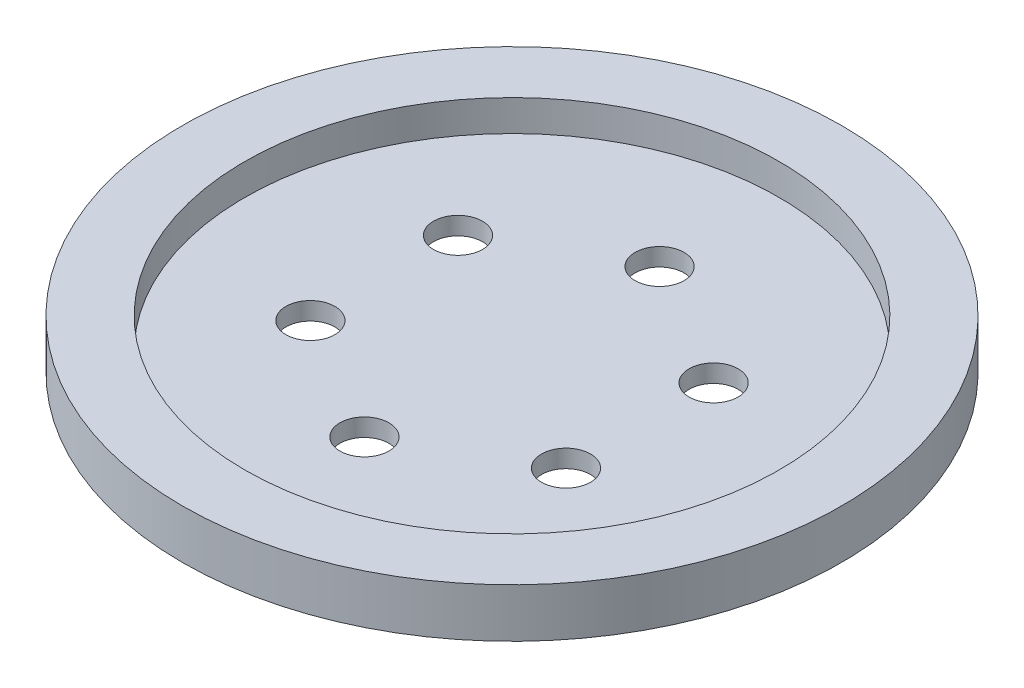
SolidWorks part; units mm, degrees
ref_plane "Front Plane" through (0, 0, 0) normal (0, 0, 1) x (1, 0, 0)
ref_plane "Top Plane" through (0, 0, 0) normal (0, 1, 0) x (1, 0, 0)
ref_plane "Right Plane" through (0, 0, 0) normal (1, 0, 0) x (0, 0, -1)
sketch "Sketch1" plane through (0, 0, 0) normal (0, 1, 0) x (1, 0, 0)
  circle A0 centre (0, 0) radius 37
  circle A1 centre (0, 16.57) radius 2.75
  circle A3 centre (-14.35, 8.285) radius 2.75
  circle A4 centre (-14.35, -8.285) radius 2.75
  circle A5 centre (0, -16.57) radius 2.75
  circle A6 centre (14.35, -8.285) radius 2.75
  circle A7 centre (14.35, 8.285) radius 2.75
  dimension "D1" = 16.57
extrude "Boss-Extrude1" add sketch "Sketch1" along normal blind 2
sketch "Sketch2" plane through (0, 2, 0) normal (0, 1, 0) x (1, 0, 0)
  circle A0 centre (0, 0) radius 37
  circle A1 centre (0, 0) radius 30
extrude "Boss-Extrude2" add sketch "Sketch2" along normal blind 3.5
